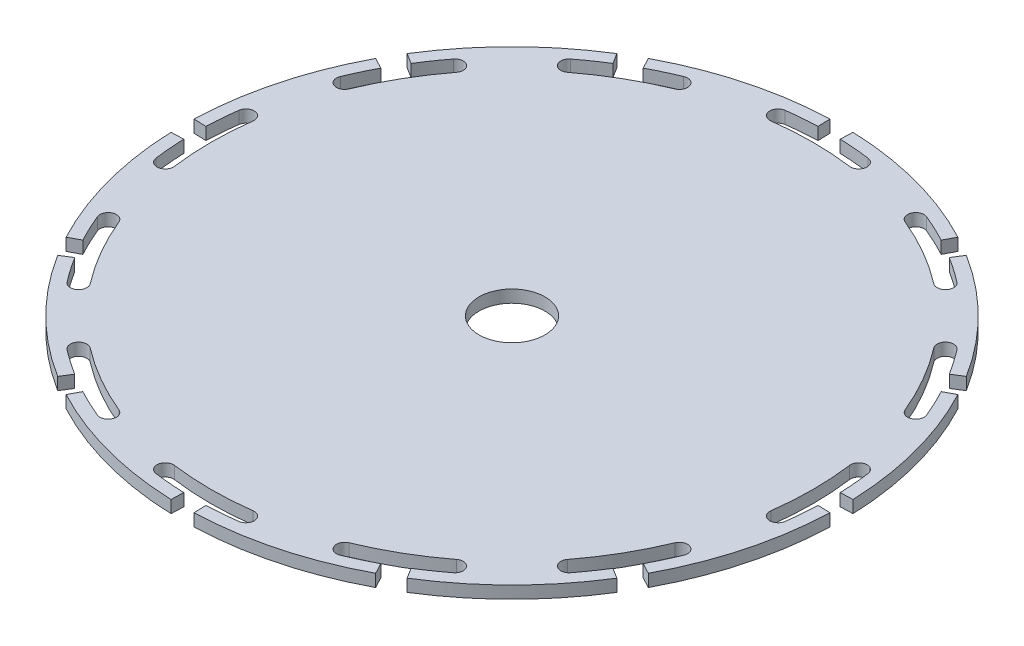
SolidWorks part; units mm, degrees
material "6061 Alloy"
ref_plane "Front Plane" through (0, 0, 0) normal (0, 0, 1) x (1, 0, 0)
ref_plane "Top Plane" through (0, 0, 0) normal (0, 1, 0) x (1, 0, 0)
ref_plane "Right Plane" through (0, 0, 0) normal (1, 0, 0) x (0, 0, -1)
sketch "Sketch1" plane through (0, 0, 0) normal (0, 1, 0) x (1, 0, 0)
  circle A0 centre (0, 0) radius 40
  dimension "D1" = 80
sketch "Sketch2" plane through (0, 0, 0) normal (0, 1, 0) x (1, 0, 0)
  line L0 (0, 0) -> (0, 40) construction
  line L1 (-1.396, 39.9756) -> (0, 0) construction
  line L2 (0, 0) -> (-5.221, 39.6578) construction
  line L3 (-1.396, 39.9756) -> (-1.3436, 38.4765)
  line L4 (0, 0) -> (5.221, 39.6578) construction
  line L5 (1.396, 39.9756) -> (0, 0) construction
  line L6 (1.396, 39.9756) -> (1.3436, 38.4765)
  arc A0 (4.7642, 36.1877) -> (-4.7642, 36.1877) centre (0, 0) ccw
  circle A1 centre (0, 0) radius 40 construction
  arc A2 (-1.396, 39.9756) -> (1.396, 39.9756) centre (0, 0) cw
  arc A3 (-1.3436, 38.4765) -> (-5.0253, 38.1706) centre (0, 0) ccw
  arc A4 (-4.7642, 36.1877) -> (-5.0253, 38.1706) centre (-4.8947, 37.1792) cw
  arc A5 (4.7642, 36.1877) -> (5.0253, 38.1706) centre (4.8947, 37.1792) ccw
  arc A6 (1.3436, 38.4765) -> (5.0253, 38.1706) centre (0, 0) cw
  point P130 (0, 0)
  dimension "D1" = 15
  dimension "D2" = 2
  dimension "D4" = 1.5
  dimension "D3" = 4
sketch "Sketch3" plane through (0, 0, 0) normal (0, 1, 0) x (1, 0, 0)
  circle A0 centre (0, 0) radius 4
  dimension "D1" = 8
extrude "Wheel Blank" add sketch "Sketch1" along normal blind 1.5
extrude "T-Slot" cut sketch "Sketch2" along normal through all
pattern_circular "CirPattern" count 12 over 360 about axis through (0, 0, 0) along (0, 1, 0) of "T-Slot"
extrude "Center Hole" cut sketch "Sketch3" along normal blind 6
